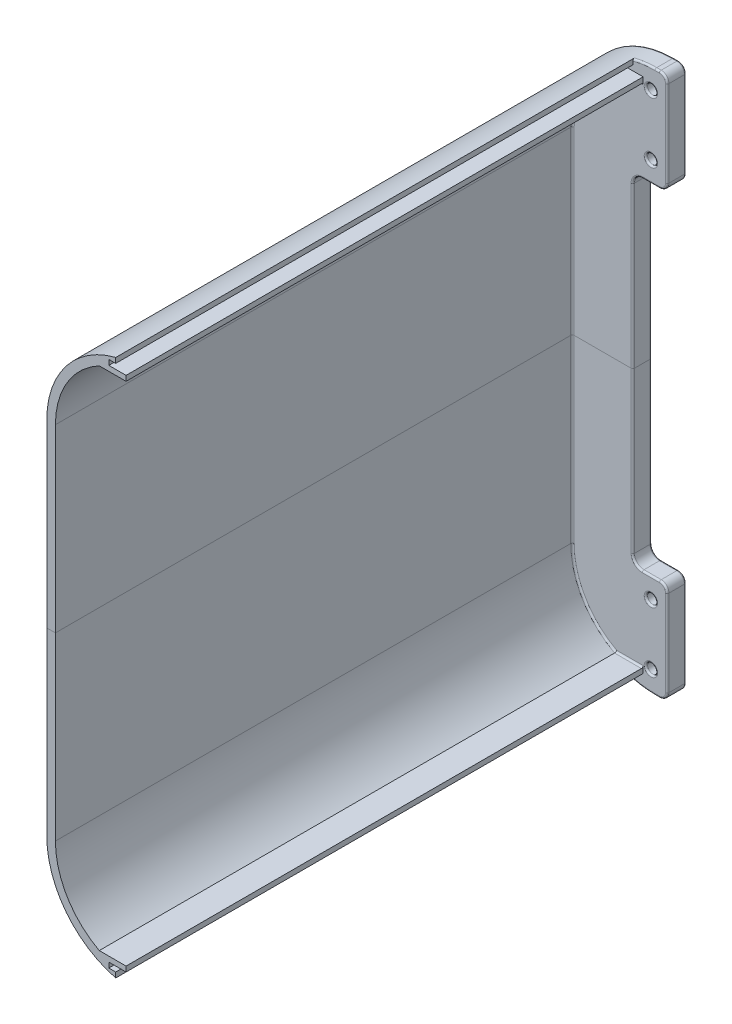
SolidWorks part; units mm, degrees
other "Side2"
other "Side1"
ref_plane "Front Plane" through (0, 0, 0) normal (0, 0, 1) x (1, 0, 0)
ref_plane "Top Plane" through (0, 0, 0) normal (0, 1, 0) x (1, 0, 0)
ref_plane "Right Plane" through (0, 0, 0) normal (1, 0, 0) x (0, 0, -1)
sketch "Sketch1" plane through (0, 0, 0) normal (0, 0, 1) x (1, 0, 0)
  line L0 (5, 111.9949) -> (-5, 111.9949) construction
  line L1 (10, 56.9949) -> (10, 106.9949) construction
  line L2 (-5, 51.9949) -> (5, 51.9949) construction
  line L3 (-10, 420) -> (-10, 0) construction
  line L4 (10, 59) -> (10, 0) construction
  line L5 (16.18, -7.7959) -> (6.8415, -23.9708) construction
  line L6 (20.1333, -8.4486) -> (18.1081, -7.2793) construction
  line L7 (33.9994, 13.5681) -> (21.4994, -8.0825) construction
  line L8 (6.2942, -24.4186) -> (3.3941, -29.4418) construction
  line L9 (5, 111.9949) -> (-5, 111.9949)
  line L10 (10, 56.9949) -> (10, 106.9949)
  line L11 (-5, 51.9949) -> (5, 51.9949)
  line L12 (-10, 420) -> (-10, 0)
  line L13 (10, 59) -> (10, 0)
  line L14 (16.18, -7.7959) -> (6.8415, -23.9708)
  line L15 (20.1333, -8.4486) -> (18.1081, -7.2793)
  line L16 (33.9994, 13.5681) -> (21.4994, -8.0825)
  line L17 (6.2942, -24.4186) -> (3.3941, -29.4418)
  line L18 (-10, 210) -> (-141.0439, 210) construction
  line L19 (0, 420) -> (0, 0) construction
  line L20 (0, 420) -> (0, 0)
  arc A0 (-10, 116.9949) -> (-5, 111.9949) centre (-5, 116.9949) ccw construction
  arc A1 (10, 106.9949) -> (5, 111.9949) centre (5, 106.9949) ccw construction
  arc A2 (5, 51.9949) -> (10, 56.9949) centre (5, 56.9949) ccw construction
  arc A3 (-5, 51.9949) -> (-10, 46.9949) centre (-5, 46.9949) ccw construction
  arc A4 (-10, 0) -> (54.641, -37.3205) centre (33.094, 0) ccw construction
  arc A5 (18.1081, -7.2793) -> (16.18, -7.7959) centre (17.1603, -7.5981) ccw construction
  arc A6 (20.1333, -8.4486) -> (21.4994, -8.0825) centre (20.6333, -7.5825) ccw construction
  arc A7 (6.8415, -23.9708) -> (6.2942, -24.4186) centre (7.1603, -24.9186) ccw construction
  arc A8 (1.8019, -29.6294) -> (3.3941, -29.4418) centre (2.528, -28.9418) ccw construction
  arc A9 (-10, 116.9949) -> (-5, 111.9949) centre (-5, 116.9949) ccw
  arc A10 (10, 106.9949) -> (5, 111.9949) centre (5, 106.9949) ccw
  arc A11 (5, 51.9949) -> (10, 56.9949) centre (5, 56.9949) ccw
  arc A12 (-5, 51.9949) -> (-10, 46.9949) centre (-5, 46.9949) ccw
  arc A13 (-10, 0) -> (54.641, -37.3205) centre (33.094, 0) ccw
  arc A14 (18.1081, -7.2793) -> (16.18, -7.7959) centre (17.1603, -7.5981) ccw
  arc A15 (20.1333, -8.4486) -> (21.4994, -8.0825) centre (20.6333, -7.5825) ccw
  arc A16 (6.8415, -23.9708) -> (6.2942, -24.4186) centre (7.1603, -24.9186) ccw
  arc A17 (1.8019, -29.6294) -> (3.3941, -29.4418) centre (2.528, -28.9418) ccw
sketch "Sketch2" plane through (0, 0, 0) normal (0, 0, 1) x (1, 0, 0)
  line L0 (9.5, 81.9949) -> (-10, 81.9949) construction
  line L1 (-10, 420) -> (-10, 0) construction
  line L2 (0, 420) -> (0, 0) construction
  line L4 (-10.5, 116.9949) -> (-10.5, 210)
  line L5 (-10, 210) -> (-141.0439, 210) construction
  line L6 (5, 52.4949) -> (-5, 52.4949)
  line L7 (9.5, 106.9949) -> (9.5, 56.9949)
  line L8 (-5, 111.4949) -> (5, 111.4949)
  line L9 (5, 52.4949) -> (2.4051, 52.4949)
  line L10 (9.5, 106.9949) -> (9.5, 56.9949)
  line L11 (-5, 111.4949) -> (5, 111.4949)
  line L12 (-50.5, 210) -> (-50.5, 105.4)
  line L13 (-141.0439, 210) -> (-10.5, 210) construction
  line L14 (-50.5, 210) -> (-10.5, 210)
  arc A0 (2.4051, 52.4949) -> (-50.5, 105.4) centre (2.4051, 105.4) cw
  circle A1 centre (0, 99.4949) radius 1.6
  circle A2 centre (0, 64.4949) radius 1.6
  arc A8 (-5, 52.4949) -> (-10.5, 46.9949) centre (-5, 46.9949) ccw
  arc A9 (5, 52.4949) -> (9.5, 56.9949) centre (5, 56.9949) ccw
  arc A10 (9.5, 106.9949) -> (5, 111.4949) centre (5, 106.9949) ccw
  arc A11 (-10.5, 116.9949) -> (-5, 111.4949) centre (-5, 116.9949) ccw
  arc A13 (5, 52.4949) -> (9.5, 56.9949) centre (5, 56.9949) ccw
  arc A14 (9.5, 106.9949) -> (5, 111.4949) centre (5, 106.9949) ccw
  arc A15 (-10.5, 116.9949) -> (-5, 111.4949) centre (-5, 116.9949) ccw
  dimension "D4" = 3.2
  dimension "D2" = 209.2
  dimension "D3" = 40
  dimension "D5" = 35
  dimension "D1" = 0.5
extrude "Boss-Extrude1" add sketch "Sketch2" along normal up to surface (11 mm away)
sketch "Sketch3" plane through (0, 0, 11) normal (0, 0, 1) x (1, 0, 0)
  circle A0 centre (0, 99.4949) radius 2.875
  circle A1 centre (0, 64.4949) radius 2.875
  dimension "D1" = 5.75
extrude "Cut-Extrude1" cut sketch "Sketch3" against normal offset from surface (9 mm away) 2 up to face at (1.6, 99.4949, 0)
sketch "Sketch4" plane through (0, 0, 11) normal (0, 0, 1) x (1, 0, 0)
  line L0 (-10, 420) -> (-10, 0) construction
  line L1 (-10.5, 54.093) -> (-10.5, 57.093)
  line L2 (-10.5, 57.093) -> (-14.5, 57.093)
  line L3 (-14.5, 57.093) -> (-14.5, 60.093)
  line L4 (-14.5, 60.093) -> (-4.5, 60.093)
  line L5 (-4.5, 60.093) -> (-4.5, 63.093)
  line L6 (-4.5, 63.093) -> (-20.0675, 63.093)
  line L7 (-45.5, 210) -> (-45.5, 105.4)
  line L8 (-50.5, 210) -> (-50.5, 105.4) construction
  line L9 (-50.5, 210) -> (-50.5, 105.4)
  line L10 (-50.5, 210) -> (-45.5, 210)
  arc A0 (-45.5, 105.4) -> (-20.0675, 63.093) centre (2.4051, 105.4) ccw
  arc A2 (-45.5, 105.4) -> (-9.2804, 58.942) centre (2.4051, 105.4) ccw construction
  arc A6 (-50.5, 105.4) -> (2.4051, 52.4949) centre (2.4051, 105.4) ccw construction
  arc A7 (-50.5, 105.4) -> (-10.5, 54.093) centre (2.4051, 105.4) ccw
  dimension "D2" = 0.5
  dimension "D4" = 3
  dimension "D5" = 3
  dimension "D6" = 4
  dimension "D7" = 10
  dimension "D1" = 5
  dimension "D3" = 5
extrude "Boss-Extrude2" add sketch "Sketch4" along normal blind 300
fillet "Fillet1" radius 1 22 edges at (-50.5, 157.7, 0) (-35.0045, 67.9904, 0) (3.7026, 52.4949, 0) (8.182, 53.8129, 0) (-10.5, 163.4974, 0) (-8.8891, 113.1058, 0) (0, 111.4949, 0) (8.182, 110.1769, 0) (3.7026, 52.4949, 11) (8.182, 53.8129, 11) (-10.5, 163.4974, 11) (-8.8891, 113.1058, 11) (0, 111.4949, 11) (8.182, 110.1769, 11) (9.5, 81.9949, 0) (2.875, 64.4949, 11) (2.875, 99.4949, 11) (9.5, 81.9949, 11) (-38.6525, 80.7185, 11) (-12.2837, 63.093, 11)
mirror "Mirror1" about plane through (-50.5, 210, 179.5463) normal (0, -1, 0) of bodies 103
delete or keep bodies "Body-Delete1" [suppressed] type delete bodies bodies 103
delete or keep bodies "Body-Delete2" [suppressed] type delete bodies bodies 104
equation "\"WindowWidth\"= 8in"
equation "\"D2@Sketch2\"=\"WindowWidth\" + 3 + 3"
equation "\"EffectorBreatingRoom\"=35"
equation "\"D3@Sketch2\"= \"EffectorBreatingRoom\" + \"WallThickness\""
equation "\"WallThickness\"= 5"
equation "\"M3ScrewDiameter\"=3.2"
equation "\"D4@Sketch2\"=\"M3ScrewDiameter\""
equation "\"M3CapheadDiameter\"=5.75"
equation "\"D1@Sketch3\"=\"M3CapheadDiameter\""
equation "\"WallHeight\"= 300"
equation "\"D1@Boss-Extrude2\"=\"WallHeight\""
